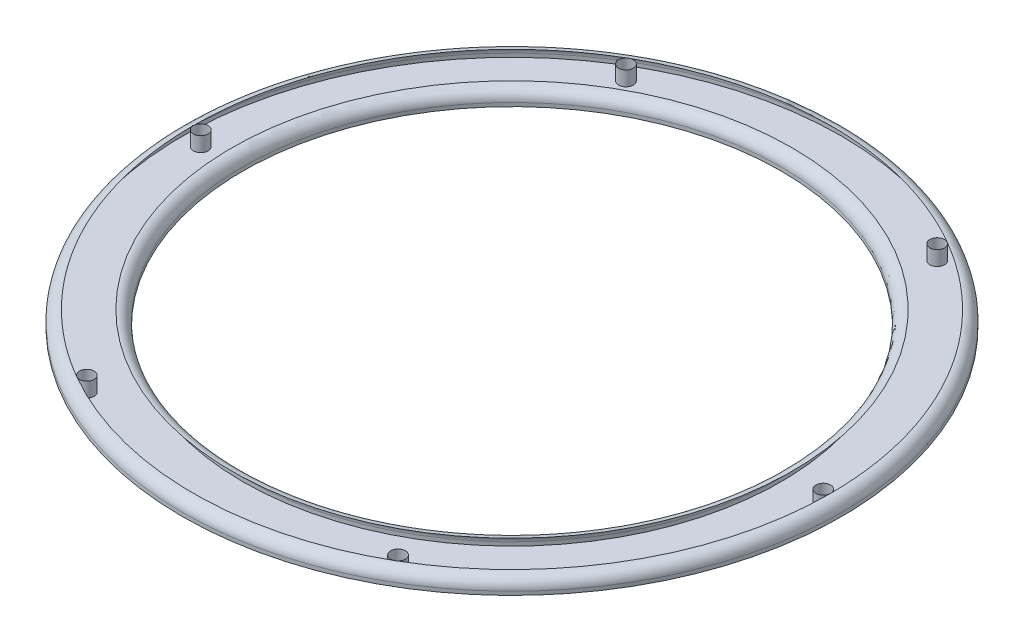
SolidWorks part; units mm, degrees
ref_plane "Front Plane" through (0, 0, 0) normal (0, 0, 1) x (1, 0, 0)
ref_plane "Top Plane" through (0, 0, 0) normal (0, 1, 0) x (1, 0, 0)
ref_plane "Right Plane" through (0, 0, 0) normal (1, 0, 0) x (0, 0, -1)
sketch "Sketch1" plane through (0, 0, 0) normal (0, 0, 1) x (1, 0, 0)
  line L0 (0, 0) -> (0, 45.0263) construction
  line L2 (-73.5, 0) -> (-90, 0)
  line L3 (-73.5, 0) -> (-73.5, 1)
  line L4 (-76.5, 4) -> (-87, 4)
  line L5 (-90, 0) -> (-90, 1)
  arc A0 (-76.5, 4) -> (-73.5, 1) centre (-76.5, 1) cw
  arc A1 (-87, 4) -> (-90, 1) centre (-87, 1) ccw
  point P11 (-90, 4)
  dimension "D4" = 3
  dimension "D1" = 4
  dimension "D2" = 147
  dimension "D3" = 180
revolve "Revolve1" add sketch "Sketch1" angle 360 about L0
sketch "Sketch2" plane through (0, 4, 0) normal (0, 1, 0) x (1, 0, 0)
  circle A0 centre (-85, 0) radius 2
  dimension "D2" = 4
  dimension "D1" = 85
extrude "Cut-Extrude1" cut sketch "Sketch2" against normal through all
pattern_circular "CirPattern1" count 6 over 360 about axis through (0, 0, 0) along (0, 1, 0) of "Cut-Extrude1"
